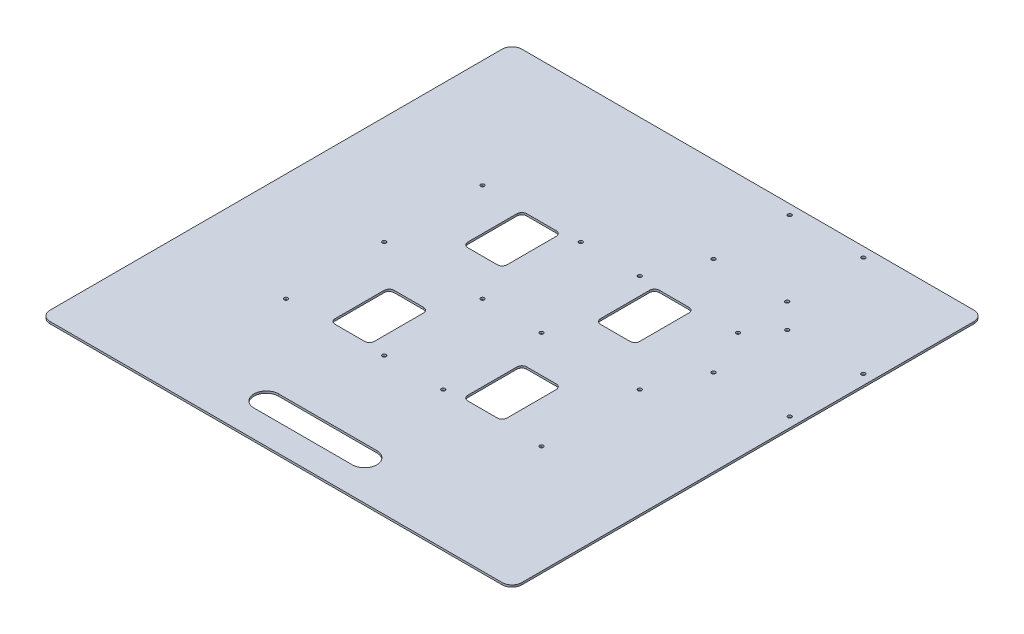
SolidWorks part; units mm, degrees
material "Plain Carbon Steel"
ref_plane "Front Plane" through (0, 0, 0) normal (0, 0, 1) x (1, 0, 0)
ref_plane "Top Plane" through (0, 0, 0) normal (0, 1, 0) x (1, 0, 0)
ref_plane "Right Plane" through (0, 0, 0) normal (1, 0, 0) x (0, 0, -1)
sketch "Sketch1" plane through (0, 0, 0) normal (0, 1, 0) x (1, 0, 0)
  line L1 (-304.8, -304.8) -> (304.8, -304.8)
  line L2 (-304.8, -304.8) -> (-304.8, 304.8)
  line L3 (-304.8, 304.8) -> (304.8, 304.8)
  line L4 (304.8, -304.8) -> (304.8, 304.8)
  line L5 (-304.8, -304.8) -> (304.8, 304.8) construction
  line L6 (-304.8, 304.8) -> (304.8, -304.8) construction
  point P0 (0, 0)
  dimension "D1" = 609.6
  dimension "D2" = 609.6
extrude "Boss-Extrude1" add sketch "Sketch1" along normal blind 2.6568
sketch "Sketch2" plane through (0, 2.6568, 0) normal (0, 1, 0) x (1, 0, 0)
  line L1 (-104.775, 123.825) -> (-66.675, 123.825)
  line L2 (-111.125, 117.475) -> (-111.125, 53.975)
  line L3 (-104.775, 47.625) -> (-66.675, 47.625)
  line L4 (-60.325, 117.475) -> (-60.325, 53.975)
  line L5 (-111.125, 123.825) -> (-60.325, 47.625) construction
  line L6 (-111.125, 47.625) -> (-60.325, 123.825) construction
  line L7 (-104.775, -47.625) -> (-66.675, -47.625)
  line L8 (-111.125, -53.975) -> (-111.125, -117.475)
  line L9 (-104.775, -123.825) -> (-66.675, -123.825)
  line L10 (-60.325, -53.975) -> (-60.325, -117.475)
  line L11 (-111.125, -47.625) -> (-60.325, -123.825) construction
  line L12 (-111.125, -123.825) -> (-60.325, -47.625) construction
  line L13 (66.675, -47.625) -> (104.775, -47.625)
  line L14 (60.325, -53.975) -> (60.325, -117.475)
  line L15 (66.675, -123.825) -> (104.775, -123.825)
  line L16 (111.125, -53.975) -> (111.125, -117.475)
  line L17 (60.325, -47.625) -> (111.125, -123.825) construction
  line L18 (60.325, -123.825) -> (111.125, -47.625) construction
  line L19 (104.775, 123.825) -> (66.675, 123.825)
  line L20 (111.125, 117.475) -> (111.125, 53.975)
  line L21 (104.775, 47.625) -> (66.675, 47.625)
  line L22 (60.325, 117.475) -> (60.325, 53.975)
  line L23 (111.125, 123.825) -> (60.325, 47.625) construction
  line L24 (111.125, 47.625) -> (60.325, 123.825) construction
  arc A0 (66.675, 47.625) -> (60.325, 53.975) centre (66.675, 53.975) cw
  arc A1 (66.675, 123.825) -> (60.325, 117.475) centre (66.675, 117.475) ccw
  arc A2 (-60.325, 117.475) -> (-66.675, 123.825) centre (-66.675, 117.475) ccw
  arc A3 (-60.325, 53.975) -> (-66.675, 47.625) centre (-66.675, 53.975) cw
  arc A4 (-104.775, 47.625) -> (-111.125, 53.975) centre (-104.775, 53.975) cw
  arc A5 (-111.125, 117.475) -> (-104.775, 123.825) centre (-104.775, 117.475) cw
  arc A6 (111.125, 117.475) -> (104.775, 123.825) centre (104.775, 117.475) ccw
  arc A7 (111.125, 53.975) -> (104.775, 47.625) centre (104.775, 53.975) cw
  arc A8 (104.775, -47.625) -> (111.125, -53.975) centre (104.775, -53.975) cw
  arc A9 (111.125, -117.475) -> (104.775, -123.825) centre (104.775, -117.475) cw
  arc A10 (66.675, -123.825) -> (60.325, -117.475) centre (66.675, -117.475) cw
  arc A11 (66.675, -47.625) -> (60.325, -53.975) centre (66.675, -53.975) ccw
  arc A12 (-60.325, -53.975) -> (-66.675, -47.625) centre (-66.675, -53.975) ccw
  arc A13 (-60.325, -117.475) -> (-66.675, -123.825) centre (-66.675, -117.475) cw
  arc A14 (-104.775, -123.825) -> (-111.125, -117.475) centre (-104.775, -117.475) cw
  arc A15 (-104.775, -47.625) -> (-111.125, -53.975) centre (-104.775, -53.975) ccw
  point P0 (-85.725, 85.725)
  point P5 (-85.725, -85.725)
  point P10 (85.725, -85.725)
  point P15 (85.725, 85.725)
  dimension "D7" = 6.35
  dimension "D8" = 6.35
  dimension "D9" = 6.35
  dimension "D1" = 85.725
  dimension "D2" = 85.725
  dimension "D3" = 85.725
  dimension "D4" = 85.725
  dimension "D5" = 76.2
  dimension "D6" = 50.8
extrude "Cut-Extrude1" cut sketch "Sketch2" against normal through all
sketch "Sketch3" plane through (0, 2.6568, 0) normal (0, 1, 0) x (1, 0, 0)
  circle A0 centre (-165.1, 127) radius 2.3876
  circle A1 centre (-165.1, 0) radius 2.3876
  circle A2 centre (-165.1, -127) radius 2.3876
  circle A3 centre (-38.1, 127) radius 2.3876
  circle A4 centre (-38.1, 0) radius 2.3876
  circle A5 centre (-38.1, -127) radius 2.3876
  dimension "D1" = 165.1
  dimension "D5" = 4.7752
  dimension "D2" = 127
  dimension "D3" = 127
  dimension "D4" = 127
extrude "Cut-Extrude2" cut sketch "Sketch3" against normal through all
pattern_linear "LPattern1" count 2 spacing 203.2 along (1, 0, 0) of "Cut-Extrude2"
sketch "Sketch4" plane through (0, 2.6568, 0) normal (0, 1, 0) x (1, 0, 0)
  line L0 (-63.5, -254) -> (63.5, -254) construction
  line L1 (-63.5, -238.125) -> (63.5, -238.125)
  line L2 (-63.5, -269.875) -> (63.5, -269.875)
  line L3 (-304.8, -304.8) -> (304.8, -304.8) construction
  arc A0 (-63.5, -238.125) -> (-63.5, -269.875) centre (-63.5, -254) ccw
  arc A1 (63.5, -269.875) -> (63.5, -238.125) centre (63.5, -254) ccw
  point P2 (0, -254)
  dimension "D1" = 31.75
  dimension "D2" = 127
  dimension "D3" = 50.8
extrude "Cut-Extrude3" cut sketch "Sketch4" against normal through all
fillet "Fillet1" radius 12.7 4 edges at (-304.8, 1.3284, -304.8) (304.8, 1.3284, -304.8) (-304.8, 1.3284, 304.8) (304.8, 1.3284, 304.8)
sketch "Sketch5" plane through (0, 2.6568, 0) normal (0, 1, 0) x (1, 0, 0)
  line L0 (304.8, -292.1) -> (304.8, 292.1) construction
  line L1 (66.675, 292.1) -> (161.925, 292.1) construction
  line L2 (66.675, 292.1) -> (66.675, 193.675) construction
  line L3 (66.675, 193.675) -> (161.925, 193.675) construction
  line L4 (161.925, 292.1) -> (161.925, 193.675) construction
  line L5 (66.675, 292.1) -> (161.925, 193.675) construction
  line L6 (66.675, 193.675) -> (161.925, 292.1) construction
  line L7 (292.1, 66.675) -> (193.675, 66.675) construction
  line L8 (292.1, 66.675) -> (292.1, 161.925) construction
  line L9 (292.1, 161.925) -> (193.675, 161.925) construction
  line L10 (193.675, 66.675) -> (193.675, 161.925) construction
  line L11 (292.1, 66.675) -> (193.675, 161.925) construction
  line L12 (292.1, 161.925) -> (193.675, 66.675) construction
  line L13 (292.1, 304.8) -> (-292.1, 304.8) construction
  circle A8 centre (161.925, 292.1) radius 2.3876
  circle A9 centre (66.675, 292.1) radius 2.3876
  circle A10 centre (161.925, 193.675) radius 2.3876
  circle A11 centre (66.675, 193.675) radius 2.3876
  circle A12 centre (193.675, 161.925) radius 2.3876
  circle A13 centre (193.675, 66.675) radius 2.3876
  circle A14 centre (292.1, 66.675) radius 2.3876
  circle A15 centre (292.1, 161.925) radius 2.3876
  point P0 (114.3, 242.8875)
  point P5 (242.8875, 114.3)
  dimension "D1" = 4.7752
  dimension "D2" = 114.3
  dimension "D3" = 114.3
  dimension "D4" = 12.7
  dimension "D5" = 12.7
  dimension "D6" = 98.425
  dimension "D7" = 95.25
extrude "Cut-Extrude4" cut sketch "Sketch5" against normal through all
sketch "Sketch6" plane through (0, 2.6568, 0) normal (0, 1, 0) x (1, 0, 0)
  point P0 (-165.1, 127)
  point P1 (-38.1, 127)
  point P3 (38.1, 127)
  point P5 (66.675, 193.675)
  point P7 (66.675, 292.1)
  point P9 (161.925, 292.1)
  point P11 (161.925, 193.675)
  point P13 (193.675, 161.925)
  point P15 (165.1, 127)
  point P17 (292.1, 161.925)
  point P19 (193.675, 66.675)
  point P21 (292.1, 66.675)
  point P23 (-165.1, 0)
  point P25 (-38.1, 0)
  point P27 (38.1, 0)
  point P29 (165.1, 0)
  point P31 (165.1, -127)
  point P32 (38.1, -127)
  point P33 (-38.1, -127)
  point P37 (-165.1, -127)
hole_wizard "#10 (0.1935) Diameter Hole1" positions "Sketch7" profile "Sketch8" hole size "#10" standard "ANSI Inch" end condition up to next
sketch "Sketch7" plane through (0, 2.6568, 0) normal (0, 1, 0) x (1, 0, 0)
  point P5 (161.925, 292.1)
  point P7 (66.675, 292.1)
  point P9 (292.1, 161.925)
  point P11 (193.675, 161.925)
  point P13 (161.925, 193.675)
  point P15 (66.675, 193.675)
  point P17 (165.1, 127)
  point P19 (38.1, 127)
  point P21 (-38.1, 127)
  point P23 (292.1, 66.675)
  point P25 (193.675, 66.675)
  point P27 (165.1, 0)
  point P29 (165.1, -127)
  point P31 (-38.1, 0)
  point P33 (38.1, 0)
  point P35 (38.1, -127)
  point P37 (-38.1, -127)
  point P39 (-165.1, -127)
  point P41 (-165.1, 0)
  point P43 (-165.1, 127)
sketch "Sketch8" plane through (161.925, 2.6568, -292.1) normal (1, 0, 0) x (0, 0, 1)
  line L0 (0, 0) -> (0, 2.6568)
  line L1 (0, 2.6568) -> (2.4574, 2.6568)
  line L2 (2.4574, 2.6568) -> (2.4574, 0)
  line L5 (2.4574, 0) -> (0, 0)
  line L11 (0, -6.35) -> (0, 107.95) construction
  dimension "Thru Hole Dia." = 4.9149
  dimension "Thru Hole Depth" = 2.6568
